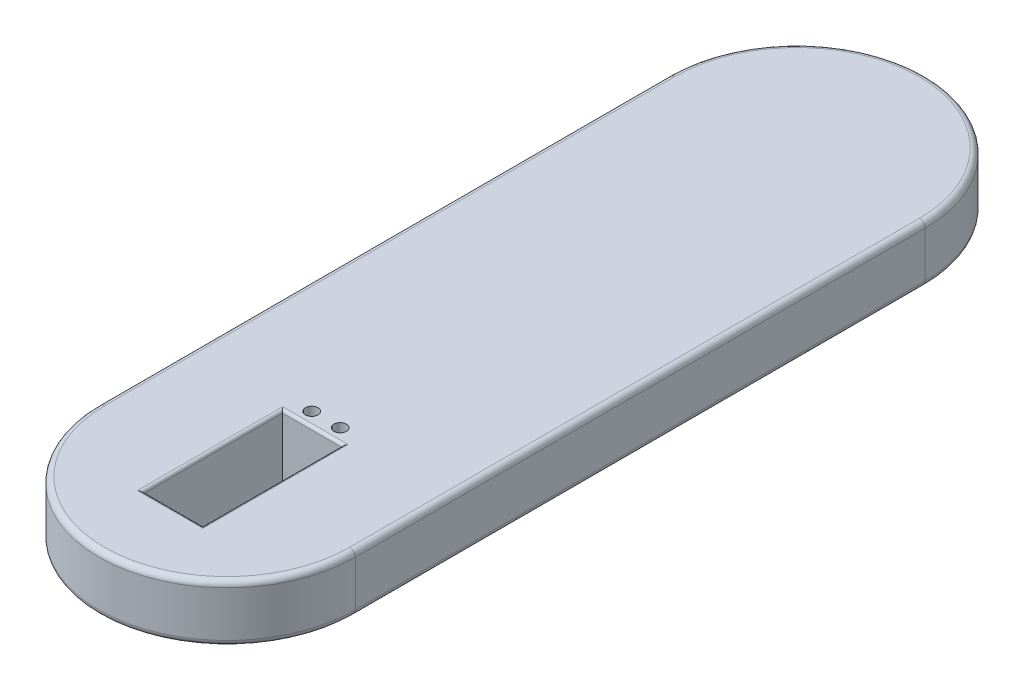
SolidWorks part; units mm, degrees
ref_plane "Front Plane" through (0, 0, 0) normal (0, 0, 1) x (1, 0, 0)
ref_plane "Top Plane" through (0, 0, 0) normal (0, 1, 0) x (1, 0, 0)
ref_plane "Right Plane" through (0, 0, 0) normal (1, 0, 0) x (0, 0, -1)
sketch "Sketch1" plane through (0, 0, 0) normal (0, 1, 0) x (1, 0, 0)
  line L0 (0, 0) -> (0, 200)
  line L1 (-90, 0) -> (-90, 200)
  arc A0 (-90, 200) -> (0, 200) centre (-45, 200) cw
  arc A1 (-90, 0) -> (0, 0) centre (-45, 0) ccw
  circle A2 centre (-50, 34.5896) radius 2.2
  circle A3 centre (-40, 34.5896) radius 2.2
  dimension "D1" = 90
  dimension "D2" = 200
  dimension "D3" = 200
extrude "Boss-Extrude1" add sketch "Sketch1" against normal blind 20
fillet "Fillet1" radius 2 8 edges at (0, -20, -100) (0, 0, -100) (-90, -20, -100) (-90, 0, -100) (-45, -20, -245) (-45, 0, -245) (-45, -20, 45) (-45, 0, 45)
sketch "Sketch4" plane through (0, -20, 0) normal (0, -1, 0) x (1, 0, 0)
  line L0 (-2, -200) -> (-89, -200) construction
  line L1 (-88, -200) -> (-90, -200) construction
  circle A0 centre (-45.5, -200) radius 11
  dimension "D1" = 22
extrude "Cut-Extrude2" cut sketch "Sketch4" against normal blind 6.35
sketch "Sketch5" plane through (0, 0, 0) normal (0, 1, 0) x (1, 0, 0)
  line L0 (-60.5, -11) -> (-60.5, 41)
  line L1 (-60.5, 41) -> (-29.5, 41)
  line L2 (-29.5, 41) -> (-29.5, -11)
  line L3 (-29.5, -11) -> (-60.5, -11)
  line L4 (-2, 0) -> (-88, 0) construction
  point P6 (-45, 0)
  point P9 (-45, 41)
  point P10 (-45, -11)
  dimension "D1" = 52
  dimension "D2" = 31
extrude "Boss-Extrude2" add sketch "Sketch5" against normal blind 36
sketch "Sketch7" plane through (0, 0, 0) normal (0, 1, 0) x (1, 0, 0)
  line L0 (-88, 0) -> (-2, 0) construction
  line L1 (-55.5, -19) -> (-55.5, 30)
  line L2 (-55.5, 30) -> (-34.5, 30)
  line L3 (-34.5, 30) -> (-34.5, -19)
  line L4 (-34.5, -19) -> (-55.5, -19)
  arc A0 (-88, 0) -> (-2, 0) centre (-45, 0) ccw construction
  point P6 (-45, 0)
  point P9 (-45, 30)
  point P10 (-45, -43)
  point P14 (-45, -19)
  dimension "D1" = 49
  dimension "D2" = 21
  dimension "D3" = 19
extrude "Cut-Extrude4" cut sketch "Sketch7" against normal blind 26
fillet "Fillet2" radius 1 4 edges at (-45, 0, 19) (-34.5, 0, -5.5) (-45, 0, -30) (-55.5, 0, -5.5)
sketch "Sketch8" plane through (0, 0, 0) normal (0, 1, 0) x (1, 0, 0)
  line L2 (-34.5, 30) -> (-55.5, 30) construction
  line L3 (-50, 34.7) -> (-40, 34.7) construction
  line L5 (-56.5, -20) -> (-56.5, 31) construction
  line L6 (-33.5, 31) -> (-33.5, -20) construction
  circle A0 centre (-50, 34.7) radius 2.2
  circle A1 centre (-40, 34.7) radius 2.2
  dimension "D1" = 4.4
  dimension "D2" = 4.4
  dimension "D3" = 6.5
  dimension "D4" = 6.5
  dimension "D5" = 4.7
  dimension "D6" = 4.7
extrude "Cut-Extrude5" cut sketch "Sketch8" against normal through all
